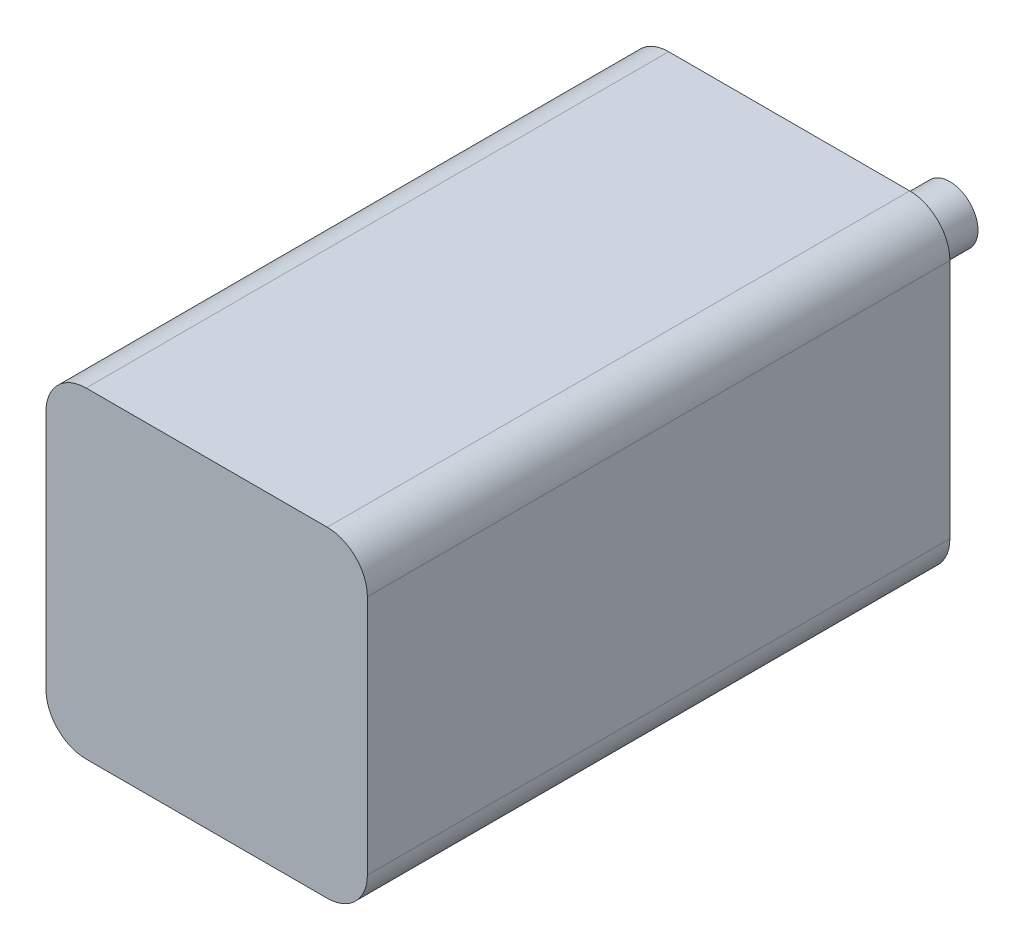
SolidWorks part; units mm, degrees
ref_plane "Front" through (0, 0, 0) normal (0, 0, 1) x (1, 0, 0)
ref_plane "Top" through (0, 0, 0) normal (0, 1, 0) x (1, 0, 0)
ref_plane "Right" through (0, 0, 0) normal (1, 0, 0) x (0, 0, -1)
other "Configuration Table"
sketch "Эскиз1" plane through (0, 0, 0) normal (0, 0, 1) x (1, 0, 0)
  line L1 (-56.4847, 18.7789) -> (23.5153, 18.7789)
  line L2 (-56.4847, 18.7789) -> (-56.4847, -61.2211)
  line L3 (-56.4847, -61.2211) -> (23.5153, -61.2211)
  line L4 (23.5153, 18.7789) -> (23.5153, -61.2211)
  dimension "D1" = 80
  dimension "D2" = 80
extrude "Бобышка-Вытянуть1" add sketch "Эскиз1" along normal blind 145
fillet "Скругление1" radius 10 4 edges at (-56.4847, -61.2211, 72.5) (23.5153, -61.2211, 72.5) (-56.4847, 18.7789, 72.5) (23.5153, 18.7789, 72.5)
sketch "Эскиз2" plane through (0, 0, 0) normal (0, 0, -1) x (-1, 0, 0)
  line L0 (56.4847, 8.7789) -> (56.4847, -51.2211) construction
  line L1 (-13.5153, 18.7789) -> (46.4847, 18.7789) construction
  circle A0 centre (16.4847, -21.2211) radius 7
  dimension "D1" = 40
  dimension "D2" = 40
extrude "Бобышка-Вытянуть2" add sketch "Эскиз2" along normal blind 40
sketch "Эскиз3" plane through (0, 0, 0) normal (0, 0, -1) x (-1, 0, 0)
  circle A0 centre (17.0218, 8.7789) radius 3.2714
  circle A1 centre (16.4847, -21.2211) radius 7 construction
  dimension "D1" = 30
extrude "Вырез-Вытянуть1" cut sketch "Эскиз3" against normal blind 10
pattern_circular "Круговой массив1" count 3 over 360 about axis through (-16.4847, -21.2211, 0) along (0, 0, 1) of "Вырез-Вытянуть1"
